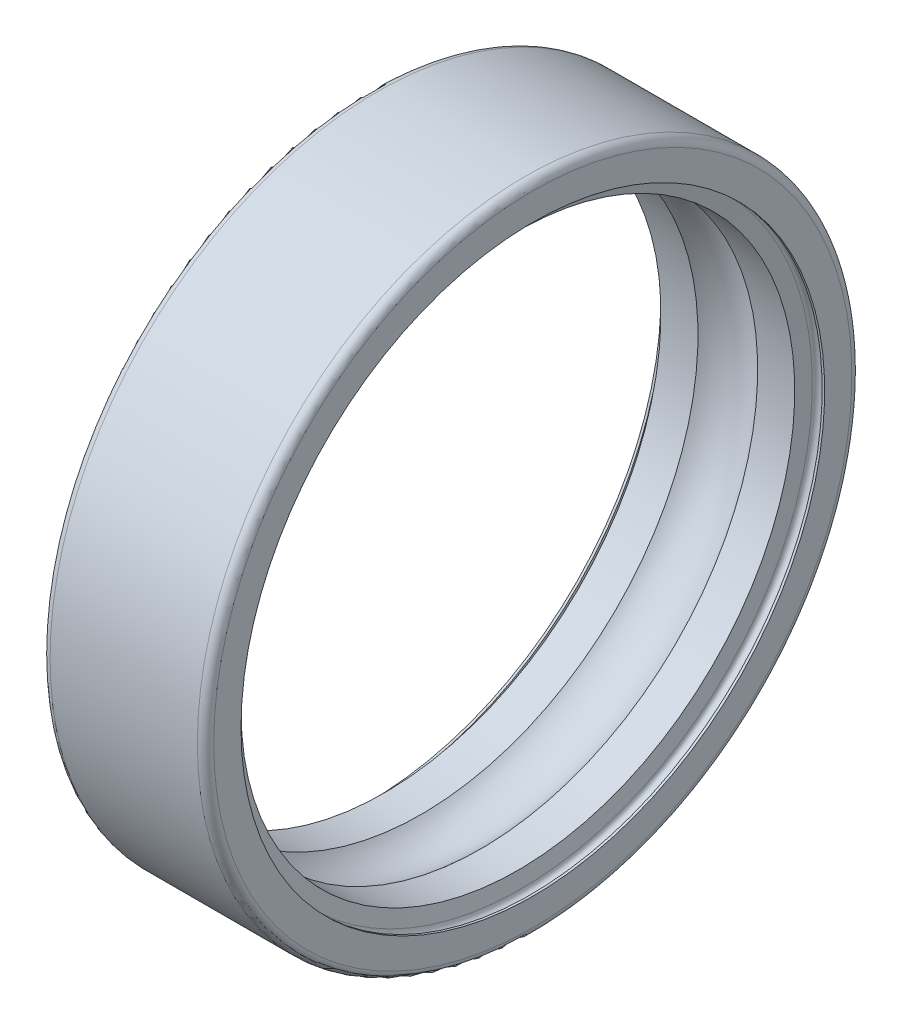
SolidWorks part; units mm, degrees
ref_plane "Front Plane" through (0, 0, 0) normal (0, 0, 1) x (1, 0, 0)
ref_plane "Top Plane" through (0, 0, 0) normal (0, 1, 0) x (1, 0, 0)
ref_plane "Right Plane" through (0, 0, 0) normal (1, 0, 0) x (0, 0, -1)
ref_plane "Plane1" through (0, 0, 0) normal (0, 0, 1) x (1, 0, 0)
sketch "Sketch1" plane through (0, 0, 0) normal (0, 0, 1) x (1, 0, 0)
  line L0 (0, 10.7) -> (0.09, 10.7)
  line L1 (0.45, 10.7) -> (0.547, 10.15)
  line L2 (0.547, 10.15) -> (1.9056, 10.15)
  line L3 (4.0944, 10.15) -> (5.453, 10.15)
  line L4 (5.453, 10.15) -> (5.55, 10.7)
  line L5 (5.91, 10.7) -> (6, 10.7)
  line L6 (6, 10.7) -> (6, 11.7)
  line L7 (5.7, 12) -> (0.3, 12)
  line L8 (0, 11.7) -> (0, 10.7)
  line L9 (50, 0) -> (-50, 0) construction
  arc A0 (0.09, 10.7) -> (0.45, 10.7) centre (0.27, 10.7) cw
  arc A1 (1.9056, 10.15) -> (4.0944, 10.15) centre (3, 9) cw
  arc A2 (5.55, 10.7) -> (5.91, 10.7) centre (5.73, 10.7) cw
  arc A3 (6, 11.7) -> (5.7, 12) centre (5.7, 11.7) ccw
  arc A4 (0.3, 12) -> (0, 11.7) centre (0.3, 11.7) ccw
revolve "Revolve1" add sketch "Sketch1" angle 360 about L9
